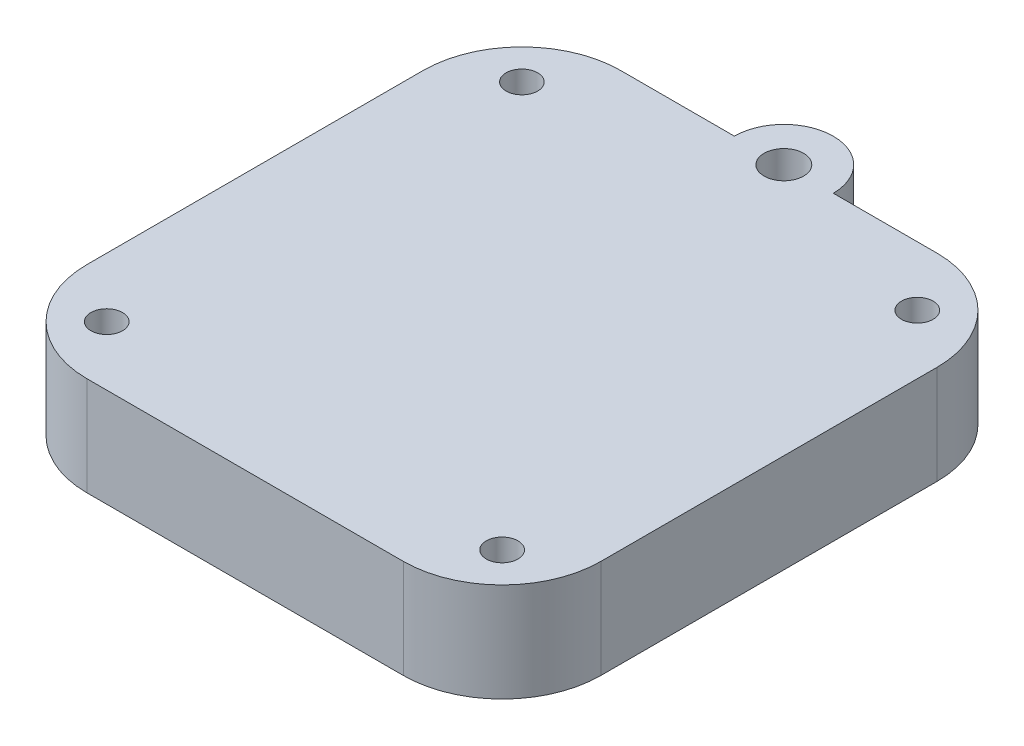
SolidWorks part; units mm, degrees
ref_plane "Front Plane" through (0, 0, 0) normal (0, 0, 1) x (1, 0, 0)
ref_plane "Top Plane" through (0, 0, 0) normal (0, 1, 0) x (1, 0, 0)
ref_plane "Right Plane" through (0, 0, 0) normal (1, 0, 0) x (0, 0, -1)
sketch "Sketch1" plane through (0, 0, 0) normal (0, 1, 0) x (1, 0, 0)
  line L0 (-4.5, 27) -> (-26, 27)
  line L1 (26, 27) -> (5.5, 27)
  line L2 (26, 27) -> (26, -27)
  line L3 (26, -27) -> (-26, -27)
  line L4 (-26, 27) -> (-26, -27)
  line L5 (26, 27) -> (-26, -27) construction
  line L6 (26, -27) -> (-26, 27) construction
  line L7 (20, 21) -> (-20, 21) construction
  line L8 (20, 21) -> (20, -21) construction
  line L9 (20, -21) -> (-20, -21) construction
  line L10 (-20, 21) -> (-20, -21) construction
  line L11 (20, 21) -> (-20, -21) construction
  line L12 (20, -21) -> (-20, 21) construction
  circle A0 centre (-20, 21) radius 1.6
  circle A1 centre (20, 21) radius 1.6
  circle A2 centre (20, -21) radius 1.6
  circle A3 centre (-20, -21) radius 1.6
  arc A4 (5.5, 27) -> (-4.5, 27) centre (0.5, 27) ccw
  circle A5 centre (0.5, 27) radius 2
  point P0 (0, 0)
  point P6 (0, 0)
  dimension "D5" = 3.2
  dimension "D6" = 10
  dimension "D7" = 4
  dimension "D1" = 52
  dimension "D2" = 54
  dimension "D3" = 40
  dimension "D4" = 42
extrude "Boss-Extrude1" add sketch "Sketch1" along normal blind 10
fillet "Fillet1" radius 10 1 edges at (-26, 5, -27)
fillet "Fillet2" radius 10 1 edges at (26, 5, -27)
fillet "Fillet3" radius 10 1 edges at (-26, 5, 27)
fillet "Fillet4" radius 10 1 edges at (26, 5, 27)
sketch "Sketch2" plane through (0, 10, 0) normal (0, 1, 0) x (1, 0, 0)
